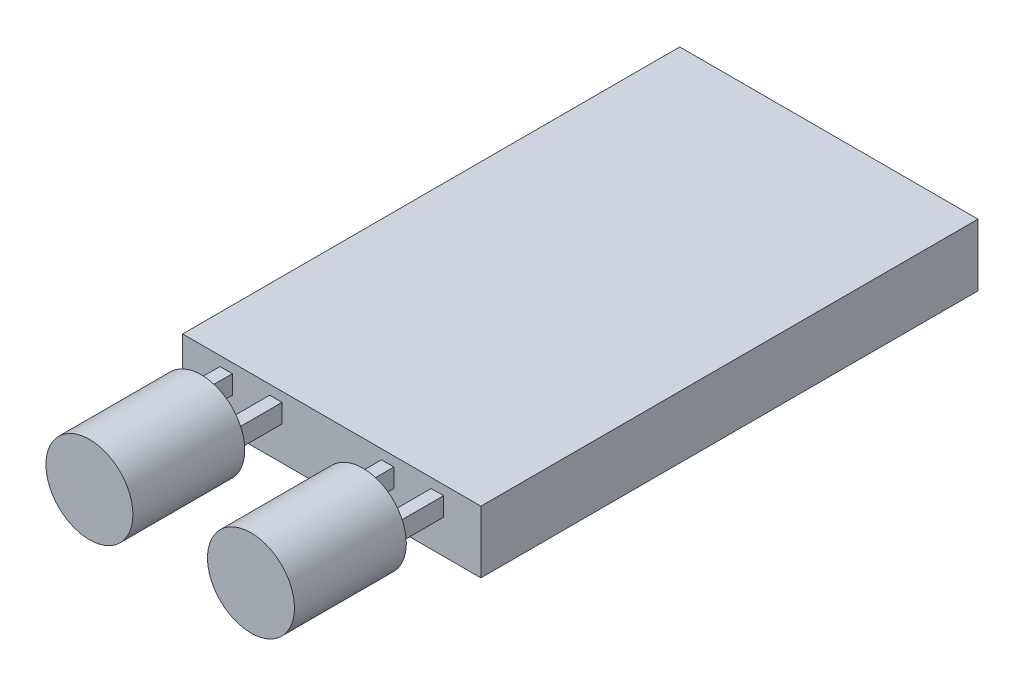
SolidWorks part; units mm, degrees
ref_plane "Front Plane" through (0, 0, 0) normal (0, 0, 1) x (1, 0, 0)
ref_plane "Top Plane" through (0, 0, 0) normal (0, 1, 0) x (1, 0, 0)
ref_plane "Right Plane" through (0, 0, 0) normal (1, 0, 0) x (0, 0, -1)
sketch "Sketch1" plane through (0, 0, 0) normal (0, 1, 0) x (1, 0, 0)
  line L1 (-24, 9.4286) -> (0, 9.4286)
  line L2 (-24, 9.4286) -> (-24, -30.5714)
  line L3 (-24, -30.5714) -> (0, -30.5714)
  line L4 (0, 9.4286) -> (0, -30.5714)
  dimension "D1" = 24
  dimension "D2" = 40
extrude "Boss-Extrude1" add sketch "Sketch1" along normal blind 5
sketch "Sketch2" plane through (0, 0, -9.4286) normal (0, 0, -1) x (-1, 0, 0)
  line L0 (0, 5) -> (0, 0) construction
  line L1 (3, 4.2295) -> (4, 4.2295)
  line L2 (3, 4.2295) -> (3, 2.7295)
  line L3 (3, 2.7295) -> (4, 2.7295)
  line L4 (4, 4.2295) -> (4, 2.7295)
  line L5 (7, 4.2295) -> (8, 4.2295)
  line L6 (7, 4.2295) -> (7, 2.7295)
  line L7 (7, 2.7295) -> (8, 2.7295)
  line L8 (8, 4.2295) -> (8, 2.7295)
  line L9 (16, 4.2295) -> (16, 2.7295)
  line L10 (16, 4.2295) -> (17, 4.2295)
  line L11 (16, 2.7295) -> (17, 2.7295)
  line L12 (17, 4.2295) -> (17, 2.7295)
  line L13 (20, 4.2295) -> (20, 2.7295)
  line L14 (20, 4.2295) -> (21, 4.2295)
  line L15 (20, 2.7295) -> (21, 2.7295)
  line L16 (21, 4.2295) -> (21, 2.7295)
  dimension "D1" = 1
  dimension "D2" = 1.5
  dimension "D3" = 1
  dimension "D4" = 1.5
  dimension "D5" = 3
  dimension "D6" = 3
  dimension "D7" = 2
extrude "Boss-Extrude5" add sketch "Sketch2" against normal blind 44
sketch "Sketch6" plane through (0, 0, 34.5714) normal (0, 0, 1) x (1, 0, 0)
  line L0 (-20, 4.2295) -> (-20, 2.7295) construction
  line L1 (-7, 4.2295) -> (-7, 2.7295) construction
  line L2 (-24, 5) -> (0, 5) construction
  circle A0 centre (-18.5, 3.4061) radius 3.5
  circle A1 centre (-5.5, 3.4) radius 3.5
  dimension "D1" = 7
  dimension "D2" = 7
  dimension "D5" = 1.5939
  dimension "D3" = 1.5
  dimension "D4" = 1.5
  dimension "D6" = 1.6
extrude "Boss-Extrude9" add sketch "Sketch6" along normal blind 9
